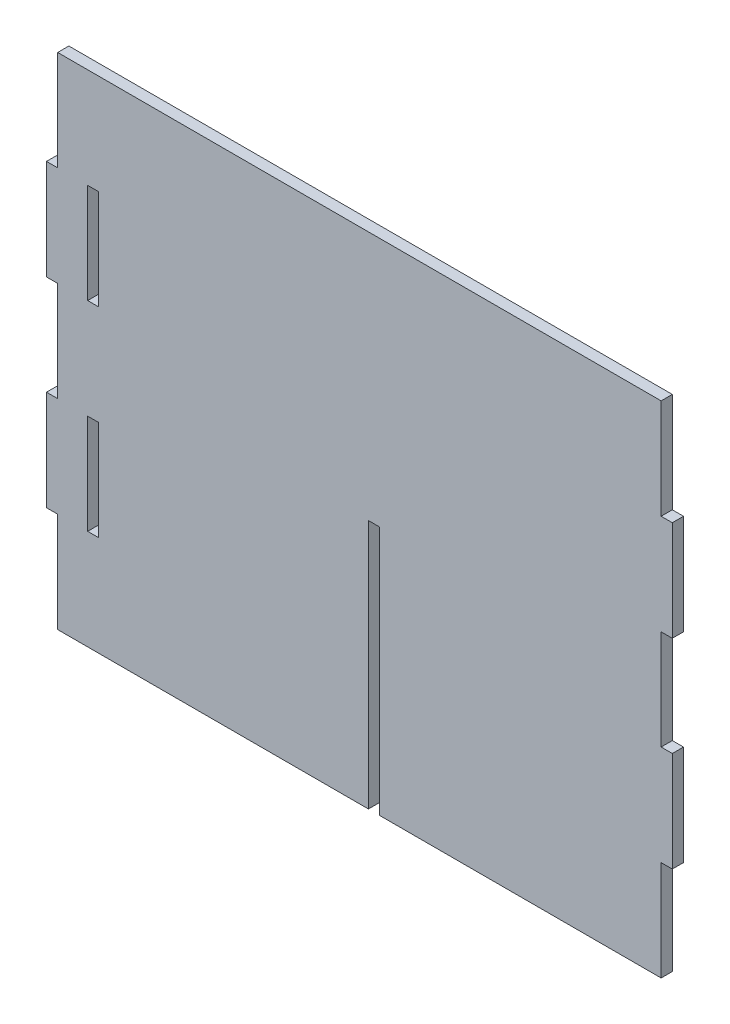
SolidWorks part; units mm, degrees
ref_plane "Front Plane" through (0, 0, 0) normal (0, 0, 1) x (1, 0, 0)
ref_plane "Top Plane" through (0, 0, 0) normal (0, 1, 0) x (1, 0, 0)
ref_plane "Right Plane" through (0, 0, 0) normal (1, 0, 0) x (0, 0, -1)
sketch "Sketch1" plane through (0, 0, 0) normal (0, 0, 1) x (1, 0, 0)
  line L0 (0, 0) -> (0, 120.6625) construction
  line L1 (145.6875, -120.6625) -> (9.7125, -120.6625)
  line L2 (145.6875, -120.6625) -> (145.6875, 120.6625)
  line L3 (145.6875, 120.6625) -> (-145.6875, 120.6625)
  line L4 (-145.6875, -120.6625) -> (-145.6875, 120.6625)
  line L5 (145.6875, -120.6625) -> (-145.6875, 120.6625) construction
  line L6 (145.6875, 120.6625) -> (-145.6875, -120.6625) construction
  line L7 (-145.6875, -72.3975) -> (-151.0875, -72.3975)
  line L8 (145.6875, 72.3975) -> (151.0875, 72.3975)
  line L9 (145.6875, 72.3975) -> (145.6875, 24.1325)
  line L10 (145.6875, 24.1325) -> (151.0875, 24.1325)
  line L11 (151.0875, 72.3975) -> (151.0875, 24.1325)
  line L12 (145.6875, -24.1325) -> (151.0875, -24.1325)
  line L13 (145.6875, -24.1325) -> (145.6875, -72.3975)
  line L14 (145.6875, -72.3975) -> (151.0875, -72.3975)
  line L15 (151.0875, -24.1325) -> (151.0875, -72.3975)
  line L16 (-151.0875, -24.1325) -> (-151.0875, -72.3975)
  line L17 (-145.6875, -24.1325) -> (-151.0875, -24.1325)
  line L18 (-145.6875, 24.1325) -> (-151.0875, 24.1325)
  line L19 (-151.0875, 72.3975) -> (-151.0875, 24.1325)
  line L20 (-145.6875, 72.3975) -> (-151.0875, 72.3975)
  line L21 (4.3125, -120.6625) -> (-145.6875, -120.6625)
  line L23 (9.7125, -120.6625) -> (9.7125, 0)
  line L24 (9.7125, 0) -> (4.3125, 0)
  line L25 (4.3125, -120.6625) -> (4.3125, 0)
  line L27 (-131.2875, 72.3975) -> (-125.8875, 72.3975)
  line L28 (-131.2875, 72.3975) -> (-131.2875, 24.1325)
  line L29 (-131.2875, 24.1325) -> (-125.8875, 24.1325)
  line L30 (-125.8875, 72.3975) -> (-125.8875, 24.1325)
  line L31 (-131.2875, -24.1325) -> (-125.8875, -24.1325)
  line L32 (-131.2875, -24.1325) -> (-131.2875, -72.3975)
  line L33 (-131.2875, -72.3975) -> (-125.8875, -72.3975)
  line L34 (-125.8875, -24.1325) -> (-125.8875, -72.3975)
  point P0 (0, 0)
  point P36 (-128.5875, 24.1325)
  dimension "D1" = 241.325
  dimension "D2" = 150
  dimension "D3" = 5.4
  dimension "D4" = 5.4
  dimension "D5" = 48.265
  dimension "D6" = 48.265
  dimension "D7" = 48.265
  dimension "D8" = 48.265
  dimension "D9" = 5.4
  dimension "D10" = 135.975
  dimension "D11" = 48.265
  dimension "D12" = 5.4
  dimension "D13" = 14.4
  dimension "D14" = 5.4
  dimension "D15" = 48.265
  dimension "D16" = 48.265
  dimension "D17" = 48.265
  dimension "D18" = 14.4
  dimension "D19" = 120.6625
extrude "Boss-Extrude1" add sketch "Sketch1" along normal blind 5.4 contours L21 L25 L24 L23 L1 L2 L3 L4 | L11 L8 L2 L10 | L15 L12 L2 L14 | L4 L20 L19 L18 | L4 L17 L16 L7
sketch "Sketch2" plane through (0, 0, 5.4) normal (0, 0, 1) x (1, 0, 0)
  line L38 (-131.2469, 24.1731) -> (-125.9281, 24.1731)
  line L39 (-125.9281, 24.1731) -> (-125.9281, 72.3569)
  line L40 (-131.2469, 72.3569) -> (-131.2469, 24.1731)
  line L41 (-125.9281, 72.3569) -> (-131.2469, 72.3569)
  line L42 (-131.2469, 24.1731) -> (-125.9281, 24.1731)
  line L43 (-125.9281, 24.1731) -> (-125.9281, 72.3569)
  line L44 (-131.2469, 72.3569) -> (-131.2469, 24.1731)
  line L45 (-125.9281, 72.3569) -> (-131.2469, 72.3569)
  line L48 (-145.7281, -120.7031) -> (4.3531, -120.7031)
  line L49 (4.3531, -120.7031) -> (4.3531, -0.0406)
  line L50 (4.3531, -0.0406) -> (9.6719, -0.0406)
  line L51 (9.6719, -0.0406) -> (9.6719, -120.7031)
  line L52 (9.6719, -120.7031) -> (145.7281, -120.7031)
  line L53 (145.7281, -120.7031) -> (145.7281, -72.4381)
  line L54 (145.7281, -72.4381) -> (151.1281, -72.4381)
  line L55 (151.1281, -72.4381) -> (151.1281, -24.0919)
  line L56 (151.1281, -24.0919) -> (145.7281, -24.0919)
  line L57 (145.7281, -24.0919) -> (145.7281, 24.0919)
  line L58 (145.7281, 24.0919) -> (151.1281, 24.0919)
  line L59 (151.1281, 24.0919) -> (151.1281, 72.4381)
  line L60 (151.1281, 72.4381) -> (145.7281, 72.4381)
  line L61 (145.7281, 72.4381) -> (145.7281, 120.7031)
  line L62 (145.7281, 120.7031) -> (-145.7281, 120.7031)
  line L63 (-145.7281, 120.7031) -> (-145.7281, 72.4381)
  line L64 (-145.7281, 72.4381) -> (-151.1281, 72.4381)
  line L65 (-151.1281, 72.4381) -> (-151.1281, 24.0919)
  line L66 (-151.1281, 24.0919) -> (-145.7281, 24.0919)
  line L67 (-145.7281, 24.0919) -> (-145.7281, -24.0919)
  line L68 (-145.7281, -24.0919) -> (-151.1281, -24.0919)
  line L69 (-151.1281, -24.0919) -> (-151.1281, -72.4381)
  line L70 (-151.1281, -72.4381) -> (-145.7281, -72.4381)
  line L71 (-145.7281, -72.4381) -> (-145.7281, -120.7031)
  line L72 (-145.7281, -120.7031) -> (4.3531, -120.7031)
  line L73 (4.3531, -120.7031) -> (4.3531, -0.0406)
  line L74 (4.3531, -0.0406) -> (9.6719, -0.0406)
  line L75 (9.6719, -0.0406) -> (9.6719, -120.7031)
  line L76 (9.6719, -120.7031) -> (145.7281, -120.7031)
  line L77 (145.7281, -120.7031) -> (145.7281, -72.4381)
  line L78 (145.7281, -72.4381) -> (151.1281, -72.4381)
  line L79 (151.1281, -72.4381) -> (151.1281, -24.0919)
  line L80 (151.1281, -24.0919) -> (145.7281, -24.0919)
  line L81 (145.7281, -24.0919) -> (145.7281, 24.0919)
  line L82 (145.7281, 24.0919) -> (151.1281, 24.0919)
  line L83 (151.1281, 24.0919) -> (151.1281, 72.4381)
  line L84 (151.1281, 72.4381) -> (145.7281, 72.4381)
  line L85 (145.7281, 72.4381) -> (145.7281, 120.7031)
  line L86 (145.7281, 120.7031) -> (-145.7281, 120.7031)
  line L87 (-145.7281, 120.7031) -> (-145.7281, 72.4381)
  line L88 (-145.7281, 72.4381) -> (-151.1281, 72.4381)
  line L89 (-151.1281, 72.4381) -> (-151.1281, 24.0919)
  line L90 (-151.1281, 24.0919) -> (-145.7281, 24.0919)
  line L91 (-145.7281, 24.0919) -> (-145.7281, -24.0919)
  line L92 (-145.7281, -24.0919) -> (-151.1281, -24.0919)
  line L93 (-151.1281, -24.0919) -> (-151.1281, -72.4381)
  line L94 (-151.1281, -72.4381) -> (-145.7281, -72.4381)
  line L95 (-145.7281, -72.4381) -> (-145.7281, -120.7031)
  line L104 (-131.2469, -72.3569) -> (-125.9281, -72.3569)
  line L105 (-125.9281, -72.3569) -> (-125.9281, -24.1731)
  line L106 (-131.2469, -24.1731) -> (-131.2469, -72.3569)
  line L107 (-125.9281, -24.1731) -> (-131.2469, -24.1731)
  line L108 (-131.2469, -72.3569) -> (-125.9281, -72.3569)
  line L109 (-125.9281, -72.3569) -> (-125.9281, -24.1731)
  line L110 (-131.2469, -24.1731) -> (-131.2469, -72.3569)
  line L111 (-125.9281, -24.1731) -> (-131.2469, -24.1731)
  dimension "D1" = 0.0406
  dimension "D2" = 0.0406
  dimension "D3" = 0.0406
extrude "Boss-Extrude2" add sketch "Sketch2" against normal up to surface (5.4 mm away) up to face at (1.1687, -10.0552, 0)
